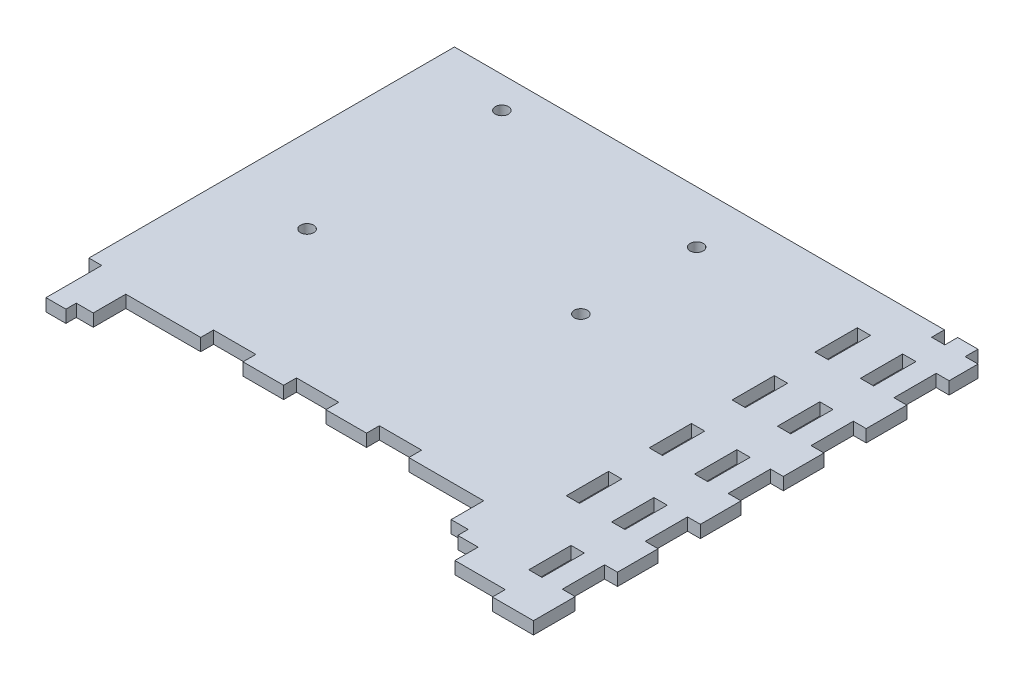
SolidWorks part; units mm, degrees
ref_plane "Front Plane" through (0, 0, 0) normal (0, 0, 1) x (1, 0, 0)
ref_plane "Top Plane" through (0, 0, 0) normal (0, 1, 0) x (1, 0, 0)
ref_plane "Right Plane" through (0, 0, 0) normal (1, 0, 0) x (0, 0, -1)
sketch "Sketch1" plane through (0, 0, 0) normal (0, 1, 0) x (1, 0, 0)
  line L0 (-129.3944, 8.1) -> (-117.3944, 8.1)
  line L1 (40.65, 8.1) -> (-69.6944, 8.1) construction
  line L2 (0, 0) -> (-129.3944, 0) construction
  line L3 (0, 0) -> (0, 110.3444) construction
  line L4 (0, 110.3444) -> (-129.3944, 110.3444)
  line L5 (-129.3944, 0) -> (-129.3944, 110.3444) construction
  line L6 (-117.3944, 19.05) -> (-31.05, 19.05)
  line L7 (-69.6944, 19.05) -> (40.65, 19.05) construction
  line L8 (-117.3944, 8.1) -> (-117.3944, 19.05)
  line L9 (-31.05, 8.1) -> (-31.05, 19.05)
  line L10 (-31.05, 8.1) -> (-22.05, 8.1)
  line L11 (-129.3944, 8.1) -> (-129.3944, 110.3444)
  line L12 (0, 110.3444) -> (0, 0)
  line L13 (-22.05, 8.1) -> (-22.05, 0)
  line L14 (-22.05, 0) -> (0, 0)
  line L15 (0, 107.4444) -> (0, 110.3444) construction
  line L17 (-74.2222, 19.05) -> (-74.2222, 0) construction
  dimension "D1" = 12
extrude "Boss-Extrude1" add sketch "Sketch1" against normal up to vertex (3 mm away)
sketch "Sketch2" plane through (0, 0, 0) normal (0, 1, 0) x (1, 0, 0)
  circle A0 centre (-58.3544, 97.7244) radius 1.5875
  circle A1 centre (-58.3544, 97.7244) radius 1.5875 construction
  circle A2 centre (-58.3544, 69.7844) radius 1.5875
  circle A4 centre (-110.4244, 102.8044) radius 1.5875
  circle A5 centre (-109.1544, 54.5444) radius 1.5875
  circle A8 centre (-58.3544, 69.7844) radius 1.5875 construction
  circle A9 centre (-110.4244, 102.8044) radius 1.5875 construction
  circle A10 centre (-109.1544, 54.5444) radius 1.5875 construction
  dimension "D1" = 3.175
extrude "Cut-Extrude1" cut sketch "Sketch2" against normal through all
sketch "Sketch3" plane through (0, 0, 0) normal (0, 1, 0) x (1, 0, 0)
  line L0 (-22.05, 8.1) -> (-22.05, 22.05) construction
  line L1 (-22.05, 22.05) -> (-129.3944, 22.05) construction
  line L2 (-22.05, 22.05) -> (-19.05, 22.05) construction
  line L3 (-19.05, 0) -> (-19.05, 110.3444) construction
  line L4 (-49.2222, 19.05) -> (-49.2222, 22.05) construction
  line L5 (-59.2222, 19.05) -> (-59.2222, 22.05) construction
  line L6 (-69.2222, 19.05) -> (-69.2222, 22.05) construction
  line L7 (-79.2222, 19.05) -> (-79.2222, 22.05) construction
  line L8 (-89.2222, 19.05) -> (-89.2222, 22.05) construction
  line L9 (-99.2222, 19.05) -> (-99.2222, 22.05) construction
  line L10 (-117.3944, 19.05) -> (-31.05, 19.05)
  line L11 (-31.05, 19.05) -> (-31.05, 8.1)
  line L12 (-31.05, 8.1) -> (-22.05, 8.1)
  line L13 (-22.05, 8.1) -> (-22.05, 0)
  line L14 (-22.05, 0) -> (0, 0)
  line L15 (0, 0) -> (0, 110.3444)
  line L16 (0, 110.3444) -> (-129.3944, 110.3444)
  line L17 (-129.3944, 110.3444) -> (-129.3944, 8.1)
  line L18 (-129.3944, 8.1) -> (-117.3944, 8.1)
  line L19 (-117.3944, 8.1) -> (-117.3944, 19.05)
  line L20 (-117.3944, 19.05) -> (-31.05, 19.05) construction
  line L21 (-31.05, 19.05) -> (-31.05, 8.1) construction
  line L22 (-31.05, 8.1) -> (-22.05, 8.1) construction
  line L23 (-22.05, 8.1) -> (-22.05, 0) construction
  line L24 (-22.05, 0) -> (0, 0) construction
  line L25 (0, 0) -> (0, 110.3444) construction
  line L26 (0, 110.3444) -> (-129.3944, 110.3444) construction
  line L27 (-129.3944, 110.3444) -> (-129.3944, 8.1) construction
  line L28 (-129.3944, 8.1) -> (-117.3944, 8.1) construction
  line L29 (-117.3944, 8.1) -> (-117.3944, 19.05) construction
  line L30 (-22.05, 22.05) -> (-22.05, 110.3444) construction
  line L31 (-11.1, 0) -> (-11.1, 110.3444) construction
  line L32 (-8.1, 0) -> (-8.1, 110.3444) construction
  line L33 (-3, 0) -> (-3, 110.3444) construction
  line L34 (0, 30.1722) -> (-3, 30.1722)
  line L35 (0, 40.1722) -> (-3, 40.1722)
  line L36 (0, 10.1722) -> (-3, 10.1722)
  line L37 (0, 20.1722) -> (-3, 20.1722)
  line L38 (0, 50.1722) -> (-3, 50.1722)
  line L39 (-22.05, 60.1722) -> (-19.05, 60.1722)
  line L40 (0, 70.1722) -> (-3, 70.1722)
  line L41 (0, 80.1722) -> (-3, 80.1722)
  line L42 (-22.05, 90.1722) -> (-19.05, 90.1722)
  line L43 (0, 100.1722) -> (-3, 100.1722)
  line L44 (0, 107.3444) -> (-3, 107.3444)
  line L45 (-10, 0) -> (-10, 3)
  line L46 (-10, 3) -> (-22.05, 3)
  line L47 (-22.05, 8.1) -> (-22.05, 8.6)
  line L48 (-22.05, 8.6) -> (-27.05, 8.6)
  line L49 (-27.05, 8.6) -> (-27.05, 11.1)
  line L50 (-27.05, 11.1) -> (-31.05, 11.1)
  line L51 (-121.3944, 8.6) -> (-121.3944, 11.1)
  line L52 (-121.3944, 11.1) -> (-117.3944, 11.1)
  line L53 (-121.3944, 8.6) -> (-126.3944, 8.6)
  line L54 (-37.35, 3) -> (0, 3) construction
  line L56 (-126.3944, 8.6) -> (-126.3944, 22.05)
  line L57 (-126.3944, 22.05) -> (-129.3944, 22.05)
  line L58 (-74.2222, 19.05) -> (-74.2222, 110.3444) construction
  line L59 (-119.3944, 11.1) -> (-119.3944, 8.1) construction
  line L60 (-19.05, 100.1722) -> (-22.05, 100.1722)
  line L61 (-11.1, 90.1722) -> (-8.1, 90.1722)
  line L62 (-19.05, 80.1722) -> (-22.05, 80.1722)
  line L63 (-19.05, 70.1722) -> (-22.05, 70.1722)
  line L64 (-11.1, 60.1722) -> (-8.1, 60.1722)
  line L65 (-19.05, 50.1722) -> (-22.05, 50.1722)
  line L66 (-19.05, 40.1722) -> (-22.05, 40.1722)
  line L67 (-19.05, 30.1722) -> (-22.05, 30.1722)
  line L68 (-8.1, 10.1722) -> (-11.1, 10.1722)
  line L69 (-8.1, 20.1722) -> (-11.1, 20.1722)
  line L70 (-8.1, 30.1722) -> (-11.1, 30.1722)
  line L71 (-8.1, 40.1722) -> (-11.1, 40.1722)
  line L72 (-8.1, 50.1722) -> (-11.1, 50.1722)
  line L73 (-3, 60.1722) -> (0, 60.1722)
  line L74 (-8.1, 70.1722) -> (-11.1, 70.1722)
  line L75 (-8.1, 80.1722) -> (-11.1, 80.1722)
  line L76 (-3, 90.1722) -> (0, 90.1722)
  line L77 (-8.1, 100.1722) -> (-11.1, 100.1722)
  line L78 (-8.1, 107.3444) -> (-11.1, 107.3444)
  dimension "D2" = 0.5
  dimension "D3" = 0.5
  dimension "D1" = 0
sketch "Sketch4" plane through (0, 0, 0) normal (0, 1, 0) x (1, 0, 0)
  line L0 (-74.2222, 19.05) -> (-74.2222, 110.3444) construction
  line L1 (-74.2222, 19.05) -> (-74.2222, 110.3444) construction
  line L2 (-126.2944, 22.15) -> (-129.4944, 22.15)
  line L3 (-69.1222, 18.95) -> (-79.3222, 18.95)
  line L4 (-69.1222, 18.95) -> (-69.1222, 22.15)
  line L5 (-69.1222, 22.15) -> (-79.3222, 22.15)
  line L6 (-79.3222, 18.95) -> (-79.3222, 22.15)
  line L7 (-89.1222, 18.95) -> (-99.3222, 18.95)
  line L8 (-89.1222, 18.95) -> (-89.1222, 22.15)
  line L9 (-89.1222, 22.15) -> (-99.3222, 22.15)
  line L10 (-99.3222, 18.95) -> (-99.3222, 22.15)
  line L11 (-129.4944, 22.15) -> (-129.4944, 8)
  line L12 (-129.4944, 8) -> (-117.2944, 8)
  line L13 (-117.2944, 8) -> (-117.2944, 11.2)
  line L14 (-117.2944, 11.2) -> (-121.4944, 11.2)
  line L15 (-121.4944, 11.2) -> (-121.4944, 8.7)
  line L16 (-121.4944, 8.7) -> (-126.2944, 8.7)
  line L17 (-126.2944, 8.7) -> (-126.2944, 22.15)
  line L18 (-69.2222, 19.05) -> (-69.3222, 19.05) construction
  line L19 (-69.3222, 19.05) -> (-69.3222, 18.95) construction
  line L20 (-69.2222, 19.05) -> (-69.1222, 19.05) construction
  line L21 (-69.2222, 22.05) -> (-69.2222, 22.15) construction
  line L22 (-89.2222, 19.05) -> (-89.1222, 19.05) construction
  line L23 (-99.2222, 19.05) -> (-99.3222, 19.05) construction
  line L24 (-117.3944, 11.1) -> (-117.3944, 11.2) construction
  line L25 (-117.3944, 11.1) -> (-117.2944, 11.1) construction
  line L26 (-121.4944, 8.7) -> (-121.4944, 8.6) construction
  line L27 (-121.4944, 8.7) -> (-121.3944, 8.7) construction
  line L28 (-121.3944, 8.6) -> (-121.3944, 11.1) construction
  line L29 (-121.3944, 8.6) -> (-126.3944, 8.6) construction
  line L30 (-129.3944, 8.1) -> (-129.3944, 8) construction
  line L31 (-129.3944, 8.1) -> (-129.4944, 8.1) construction
  line L32 (-126.2944, 8.7) -> (-126.3944, 8.7) construction
  line L33 (-126.3944, 8.6) -> (-126.3944, 22.05) construction
  line L34 (-59.3222, 18.95) -> (-59.3222, 22.15)
  line L35 (-59.3222, 18.95) -> (-49.1222, 18.95)
  line L36 (-49.1222, 18.95) -> (-49.1222, 22.15)
  line L37 (-59.3222, 22.15) -> (-49.1222, 22.15)
  line L38 (-26.95, 8.7) -> (-22.05, 8.7)
  line L39 (-26.95, 11.2) -> (-26.95, 8.7)
  line L40 (-31.15, 11.2) -> (-26.95, 11.2)
  line L41 (-31.15, 8) -> (-31.15, 11.2)
  line L42 (-22.05, 8) -> (-31.15, 8)
  line L43 (-22.05, 8.7) -> (-22.05, 8)
  line L44 (-22.05, 8.1) -> (-22.05, 8.6) construction
  line L45 (-11.2, 30.0722) -> (-11.2, 40.2722)
  line L46 (-9.9, -0.1) -> (-22.15, -0.1)
  line L47 (-9.9, -0.1) -> (-9.9, 3.1)
  line L48 (-9.9, 3.1) -> (-22.15, 3.1)
  line L49 (-22.15, -0.1) -> (-22.15, 3.1)
  line L50 (-11.2, 10.0722) -> (-8, 10.0722)
  line L51 (-11.2, 10.0722) -> (-11.2, 20.2722)
  line L52 (-11.2, 20.2722) -> (-8, 20.2722)
  line L53 (0.1, 10.0722) -> (0.1, 20.2722)
  line L54 (0.1, 30.0722) -> (-3.1, 30.0722)
  line L55 (0.1, 30.0722) -> (0.1, 40.2722)
  line L56 (0.1, 40.2722) -> (-3.1, 40.2722)
  line L57 (-22.15, 30.0722) -> (-22.15, 40.2722)
  line L58 (0.1, 50.0722) -> (-3.1, 50.0722)
  line L59 (0.1, 50.0722) -> (0.1, 60.2722)
  line L60 (0.1, 60.2722) -> (-3.1, 60.2722)
  line L61 (-22.15, 50.0722) -> (-22.15, 60.2722)
  line L62 (0.1, 70.0722) -> (-3.1, 70.0722)
  line L63 (0.1, 70.0722) -> (0.1, 80.2722)
  line L64 (0.1, 80.2722) -> (-3.1, 80.2722)
  line L65 (-22.15, 70.0722) -> (-22.15, 80.2722)
  line L66 (0.1, 90.0722) -> (-3.1, 90.0722)
  line L67 (0.1, 90.0722) -> (0.1, 100.2722)
  line L68 (0.1, 100.2722) -> (-3.1, 100.2722)
  line L69 (-22.15, 90.0722) -> (-22.15, 100.2722)
  line L70 (-11.2, 107.2444) -> (-8, 107.2444)
  line L71 (-11.2, 107.2444) -> (-11.2, 110.4444)
  line L72 (-11.2, 110.4444) -> (-8, 110.4444)
  line L73 (0.1, 107.2444) -> (0.1, 110.4444)
  line L74 (-8, 10.0722) -> (-8, 20.2722)
  line L75 (-18.95, 30.0722) -> (-18.95, 40.2722)
  line L76 (-3.1, 10.0722) -> (-3.1, 20.2722)
  line L77 (-10, 0) -> (-9.9, 0) construction
  line L78 (-22.05, 0) -> (0, 0) construction
  line L79 (-10, 0) -> (-10, -0.1) construction
  line L80 (-22.05, 3) -> (-22.05, 3.1) construction
  line L81 (-22.05, 3) -> (-22.15, 3) construction
  line L82 (0, 10.1722) -> (0.1, 10.1722) construction
  line L83 (-3, 10.1722) -> (-3.1, 10.1722) construction
  line L84 (-8.1, 10.1722) -> (-8, 10.1722) construction
  line L85 (-11.1, 10.1722) -> (-11.2, 10.1722) construction
  line L86 (0, 10.1722) -> (0, 10.0722) construction
  line L87 (0, 20.1722) -> (0, 20.2722) construction
  line L88 (0, 30.1722) -> (0, 30.0722) construction
  line L89 (-19.05, 30.1722) -> (-18.95, 30.1722) construction
  line L90 (-22.05, 30.1722) -> (-22.15, 30.1722) construction
  line L91 (0, 40.1722) -> (0, 40.2722) construction
  line L92 (0, 50.1722) -> (0, 50.0722) construction
  line L93 (0, 60.1722) -> (0, 60.2722) construction
  line L94 (0, 70.1722) -> (0, 70.0722) construction
  line L95 (0, 80.1722) -> (0, 80.2722) construction
  line L96 (0, 90.1722) -> (0, 90.0722) construction
  line L97 (0, 100.1722) -> (0, 100.2722) construction
  line L98 (0, 107.3444) -> (0, 107.2444) construction
  line L99 (0, 110.3444) -> (0, 110.4444) construction
  line L100 (-3.1, 110.4444) -> (0.1, 110.4444)
  line L101 (-3.1, 107.2444) -> (0.1, 107.2444)
  line L102 (-3.1, 107.2444) -> (-3.1, 110.4444)
  line L103 (-8, 107.2444) -> (-8, 110.4444)
  line L104 (-18.95, 100.2722) -> (-22.15, 100.2722)
  line L105 (-8, 100.2722) -> (-11.2, 100.2722)
  line L106 (-8, 90.0722) -> (-11.2, 90.0722)
  line L107 (-18.95, 90.0722) -> (-22.15, 90.0722)
  line L108 (-18.95, 90.0722) -> (-18.95, 100.2722)
  line L109 (-11.2, 90.0722) -> (-11.2, 100.2722)
  line L110 (-8, 90.0722) -> (-8, 100.2722)
  line L111 (-3.1, 90.0722) -> (-3.1, 100.2722)
  line L112 (-8, 80.2722) -> (-11.2, 80.2722)
  line L113 (-18.95, 80.2722) -> (-22.15, 80.2722)
  line L114 (-8, 40.2722) -> (-11.2, 40.2722)
  line L115 (-18.95, 40.2722) -> (-22.15, 40.2722)
  line L116 (-18.95, 50.0722) -> (-18.95, 60.2722)
  line L117 (-11.2, 50.0722) -> (-11.2, 60.2722)
  line L118 (-8, 50.0722) -> (-8, 60.2722)
  line L119 (-3.1, 50.0722) -> (-3.1, 60.2722)
  line L120 (-8, 50.0722) -> (-11.2, 50.0722)
  line L121 (-8, 60.2722) -> (-11.2, 60.2722)
  line L122 (-3.1, 70.0722) -> (-3.1, 80.2722)
  line L123 (-8, 70.0722) -> (-8, 80.2722)
  line L124 (-11.2, 70.0722) -> (-11.2, 80.2722)
  line L125 (-18.95, 60.2722) -> (-22.15, 60.2722)
  line L126 (-18.95, 50.0722) -> (-22.15, 50.0722)
  line L127 (-18.95, 70.0722) -> (-22.15, 70.0722)
  line L128 (-8, 70.0722) -> (-11.2, 70.0722)
  line L129 (-3.1, 10.0722) -> (0.1, 10.0722)
  line L130 (-3.1, 20.2722) -> (0.1, 20.2722)
  line L131 (-3.1, 30.0722) -> (-3.1, 40.2722)
  line L132 (-8, 30.0722) -> (-8, 40.2722)
  line L133 (-8, 30.0722) -> (-11.2, 30.0722)
  line L134 (-18.95, 30.0722) -> (-22.15, 30.0722)
  line L135 (-18.95, 70.0722) -> (-18.95, 80.2722)
  line L136 (-3, 0) -> (-3, 110.3444) construction
extrude "Cut-Extrude2" cut sketch "Sketch4" against normal through all
